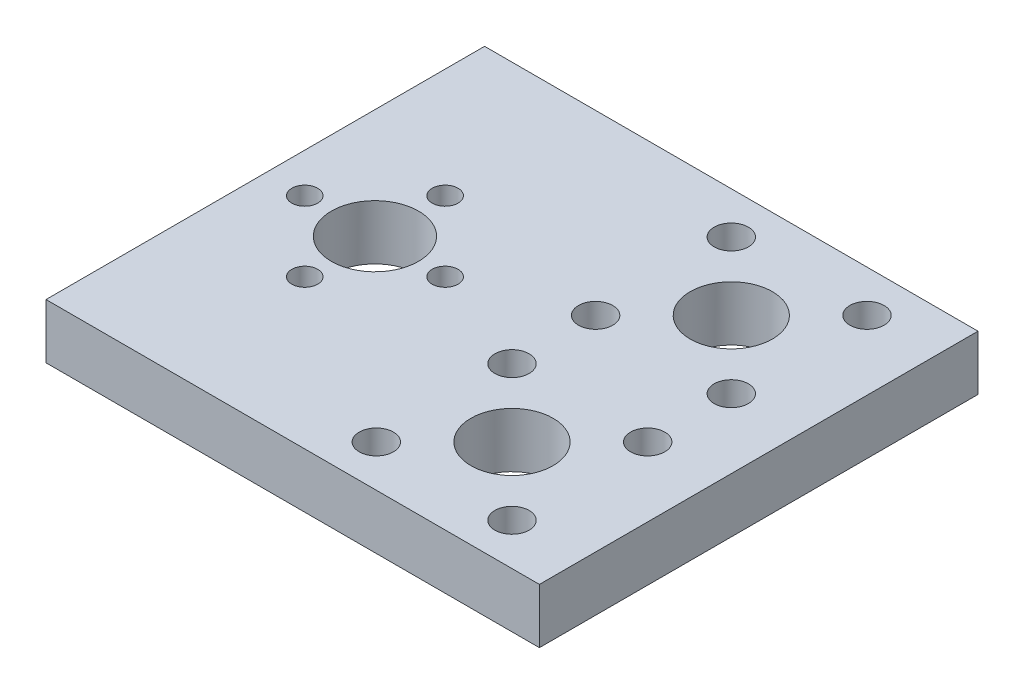
SolidWorks part; units mm, degrees
material "AISI 1020"
ref_plane "Front Plane" through (0, 0, 0) normal (0, 0, 1) x (1, 0, 0)
ref_plane "Top Plane" through (0, 0, 0) normal (0, 1, 0) x (1, 0, 0)
ref_plane "Right Plane" through (0, 0, 0) normal (1, 0, 0) x (0, 0, -1)
sketch "Sketch3" plane through (0, 0, 0) normal (0, 0, 1) x (1, 0, 0)
  line L0 (-121.2197, 0) -> (-64.0697, 0)
  line L6 (-64.0697, -6.35) -> (-121.2197, -6.35)
  line L7 (-121.2197, -6.35) -> (-121.2197, 0)
  line L10 (-64.0697, -6.35) -> (-64.0697, 0)
  dimension "D2" = 6.35
  dimension "D4" = 57.15
extrude "Boss-Extrude2" add sketch "Sketch3" along normal blind 50.8
sketch "Sketch4" plane through (0, 0, 0) normal (0, 1, 0) x (1, 0, 0)
  line L0 (-121.2197, -50.8) -> (-121.2197, 0) construction
  line L1 (-68.8322, -49.2125) -> (-91.0572, -49.2125) construction
  line L2 (-68.8322, -49.2125) -> (-68.8322, -26.9875) construction
  line L3 (-68.8322, -26.9875) -> (-91.0572, -26.9875) construction
  line L4 (-121.2197, -25.4) -> (-62.5425, -25.4) construction
  line L5 (-64.0697, 0) -> (-121.2197, 0) construction
  line L6 (-79.9447, -38.1) -> (-79.9447, -12.7) construction
  line L7 (-91.0572, -49.2125) -> (-91.0572, -26.9875) construction
  line L8 (-68.8322, -49.2125) -> (-91.0572, -26.9875) construction
  line L9 (-68.8322, -26.9875) -> (-91.0572, -49.2125) construction
  line L10 (-68.8322, -23.8125) -> (-91.0572, -1.5875) construction
  line L12 (-68.8322, -1.5875) -> (-91.0572, -23.8125) construction
  line L13 (-91.0572, -1.5875) -> (-91.0572, -23.8125) construction
  line L14 (-68.8322, -23.8125) -> (-91.0572, -23.8125) construction
  line L15 (-68.8322, -1.5875) -> (-68.8322, -23.8125) construction
  line L16 (-68.8322, -1.5875) -> (-91.0572, -1.5875) construction
  circle A0 centre (-108.5197, -25.4) radius 5.05
  circle A5 centre (-79.9447, -38.1) radius 4.7625
  circle A6 centre (-79.9447, -38.1) radius 11.1125 construction
  circle A17 centre (-108.5197, -17.27) radius 1.5
  circle A18 centre (-87.8024, -30.2423) radius 1.9844
  circle A19 centre (-72.0869, -30.2423) radius 1.9844
  circle A20 centre (-72.0869, -45.9577) radius 1.9844
  circle A21 centre (-87.8024, -45.9577) radius 1.9844
  circle A22 centre (-116.6497, -25.4) radius 1.5
  circle A26 centre (-100.3897, -25.4) radius 1.5
  circle A27 centre (-108.5197, -33.53) radius 1.5
  circle A29 centre (-79.9447, -12.7) radius 11.1125 construction
  circle A30 centre (-87.8024, -4.8423) radius 1.9844
  circle A31 centre (-72.0869, -4.8423) radius 1.9844
  circle A32 centre (-72.0869, -20.5577) radius 1.9844
  circle A33 centre (-87.8024, -20.5577) radius 1.9844
  circle A34 centre (-79.9447, -12.7) radius 4.7625
  point P13 (-91.8811, -25.4)
  point P50 (-62.5425, -25.4)
  dimension "D1" = 10.1
  dimension "D2" = 25.4
  dimension "D3" = 22.225
  dimension "D4" = 11.1125
  dimension "D5" = 9.525
  dimension "D7" = 4
  dimension "D6" = 3.9688
  dimension "D8" = 3
  dimension "D13" = 8.13
  dimension "D9" = 8.13
  dimension "D11" = 12.7
  dimension "D12" = 8.13
  dimension "D10" = 28.575
extrude "Cut-Extrude1" cut sketch "Sketch4" against normal up to surface (6.35 mm away) up to face at (-92.6447, -6.35, 25.4)
